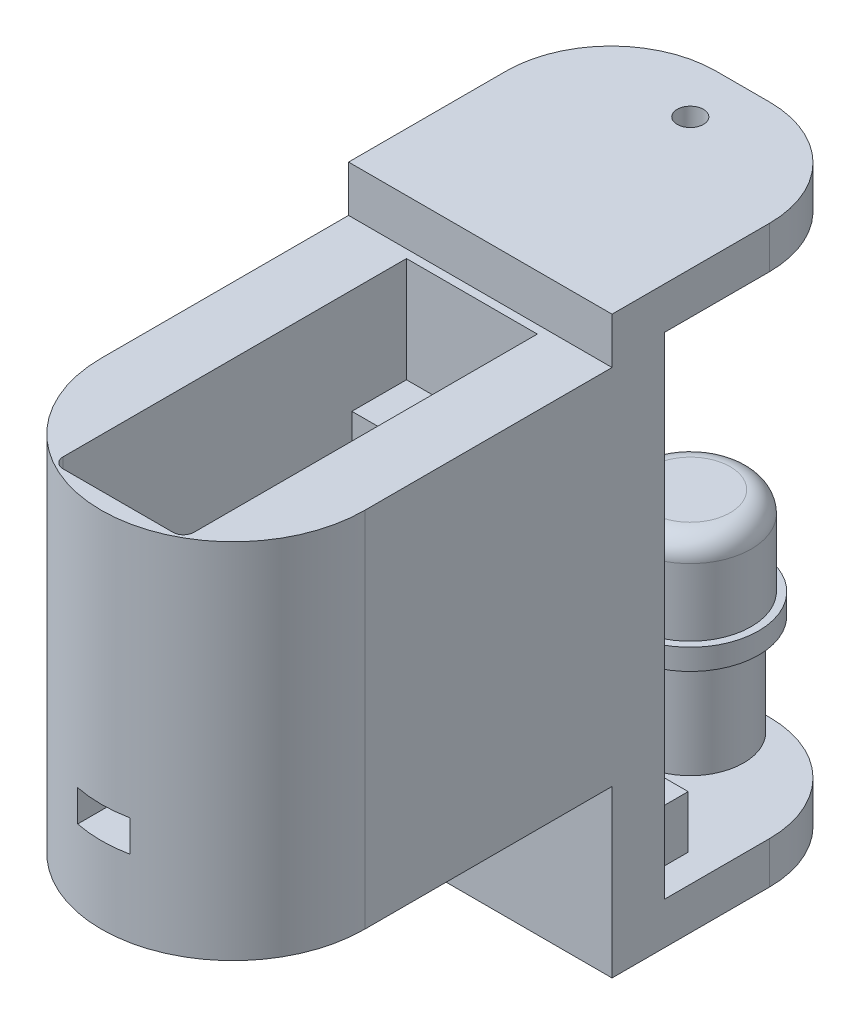
SolidWorks part; units mm, degrees
ref_plane "Front Plane" through (0, 0, 0) normal (0, 0, 1) x (1, 0, 0)
ref_plane "Top Plane" through (0, 0, 0) normal (0, 1, 0) x (1, 0, 0)
ref_plane "Right Plane" through (0, 0, 0) normal (1, 0, 0) x (0, 0, -1)
sketch "Sketch4" plane through (0, 0, 0) normal (0, 0, 1) x (1, 0, 0)
  line L1 (-6.23, -9.975) -> (6.23, -9.975)
  line L2 (-6.23, -9.975) -> (-6.23, 7.275)
  line L3 (-6.23, 7.275) -> (6.23, 7.275)
  line L4 (6.23, -9.975) -> (6.23, 7.275)
  point P4 (0, 7.275)
  dimension "D1" = 12.46
  dimension "D2" = 17.25
  dimension "D3" = 9.975
extrude "Boss-Extrude3" add sketch "Sketch4" along normal blind 6
sketch "Sketch8" plane through (0, -9.975, 0) normal (0, -1, 0) x (-1, 0, 0)
  circle A0 centre (0, -23.55) radius 12.5468
  circle A1 centre (0, -23.55) radius 11.15
  dimension "D1" = 22.3
  dimension "D2" = 23.55
extrude "Boss-Extrude6" add sketch "Sketch8" along normal blind 7.3 and the other way up to surface (17.25 mm away) other way up to face at (0, 7.275, 3)
sketch "Sketch5" plane through (0, 7.275, 0) normal (0, 1, 0) x (1, 0, 0)
  line L8 (12.5468, -23.55) -> (12.5468, 0)
  line L9 (12.5468, 0) -> (6.23, 0)
  line L10 (-12.5468, -23.55) -> (-12.5468, 0)
  line L11 (-12.5468, 0) -> (-6.23, 0)
  line L12 (-6.23, 0) -> (-6.23, -29.7)
  line L14 (6.23, -29.7) -> (6.23, 0)
  line L15 (-6.23, -29.7) -> (6.23, -29.7)
  line L16 (6.23, -6) -> (-6.23, -6) construction
  circle A0 centre (0, -23.55) radius 12.5468 construction
  arc A1 (-12.5468, -23.55) -> (12.5468, -23.55) centre (0, -23.55) ccw
  dimension "D1" = 23.7
  dimension "D2" = 23.55
extrude "Boss-Extrude4" add sketch "Sketch5" against normal up to surface (17.25 mm away) up to face at (0, -9.975, 3)
sketch "Sketch6" plane through (0, 7.275, 0) normal (0, 1, 0) x (1, 0, 0)
  line L0 (6.23, -6) -> (-6.23, -6) construction
  line L3 (6.23, -29.7) -> (-6.23, -29.7) construction
  circle A0 centre (0, -3.6) radius 0.5
  circle A1 centre (0, -32.1) radius 0.5
  dimension "D1" = 1
  dimension "D3" = 1
  dimension "D2" = 2.4
  dimension "D4" = 2.4
extrude "Cut-Extrude1" cut sketch "Sketch6" against normal blind 15
chamfer "Chamfer1" distance 0.5 angle 60 2 edges at (0, 7.275, 4.1) (0, 7.275, 32.6)
sketch "Sketch10" plane through (0, 7.275, 0) normal (0, 1, 0) x (1, 0, 0)
  line L1 (-6.23, -6) -> (6.23, -6)
  line L2 (-6.23, -6) -> (-6.23, -29.7)
  line L3 (-6.23, -29.7) -> (6.23, -29.7)
  line L4 (6.23, -6) -> (6.23, -29.7)
extrude "Cut-Extrude3" cut sketch "Sketch10" against normal up to surface (17.25 mm away) up to face at (0, -9.975, 27.1007)
ref_plane "Plane1" through (0, 0, 36.0968) normal (0, 0, 1) x (1, 0, 0)
sketch "Sketch11" plane through (0, 0, 36.0968) normal (0, 0, 1) x (1, 0, 0)
  line L0 (-11.15, -9.975) -> (11.15, -9.975) construction
  line L1 (-2.5, -6.975) -> (2.5, -6.975)
  line L2 (-2.5, -6.975) -> (-2.5, -9.975)
  line L3 (-2.5, -9.975) -> (2.5, -9.975)
  line L4 (2.5, -6.975) -> (2.5, -9.975)
  point P4 (0, -6.975)
  dimension "D1" = 0
  dimension "D2" = 5
  dimension "D3" = 3
extrude "Cut-Extrude4" cut sketch "Sketch11" against normal up to next
sketch "Sketch13" plane through (0, -17.275, 0) normal (0, -1, 0) x (1, 0, 0)
  line L0 (-12.5468, 23.55) -> (-12.5468, 0)
  line L1 (-12.5468, 0) -> (12.5468, 0)
  line L2 (12.5468, 0) -> (12.5468, 23.55)
  arc A0 (-12.5468, 23.55) -> (12.5468, 23.55) centre (0, 23.55) ccw
  point P3 (0, 0)
extrude "Boss-Extrude7" add sketch "Sketch13" against normal up to surface (7.3 mm away) up to face at (6.0145, -9.975, 27.3356)
sketch "Sketch15" plane through (0, 7.275, 0) normal (0, 1, 0) x (1, 0, 0)
  line L0 (-12.5468, 0) -> (12.5468, 0)
  line L1 (12.5468, 0) -> (12.5468, -23.55)
  line L2 (-12.5468, 0) -> (-12.5468, -23.55)
  line L3 (6.23, -6) -> (6.23, -29.7) construction
  line L4 (-6.23, -0.8) -> (6.23, -0.8)
  line L5 (-6.23, -0.8) -> (-6.23, -33.5)
  line L6 (-5.23, -34.5) -> (5.23, -34.5)
  line L7 (6.23, -0.8) -> (6.23, -33.5)
  arc A0 (-12.5468, -23.55) -> (12.5468, -23.55) centre (0, -23.55) ccw
  circle A1 centre (0, -3.6) radius 0.5 construction
  arc A2 (5.23, -34.5) -> (6.23, -33.5) centre (5.23, -33.5) ccw
  arc A3 (-6.23, -33.5) -> (-5.23, -34.5) centre (-5.23, -33.5) ccw
  point P15 (0, -0.8)
  dimension "D1" = 0.8
  dimension "D3" = 1
  dimension "D2" = 2.8
  dimension "D4" = 0
  dimension "D5" = 34.5
extrude "Boss-Extrude9" add sketch "Sketch15" along normal blind 10
sketch "Sketch20" plane through (0, -17.275, 0) normal (0, -1, 0) x (1, 0, 0)
  circle A0 centre (0, 23.55) radius 7.15
  circle A1 centre (0, 23.55) radius 11.15
  circle A2 centre (0, 23.55) radius 11.15 construction
  dimension "D1" = 14.3
extrude "Boss-Extrude11" add sketch "Sketch20" against normal up to surface (7.3 mm away) up to face at (-6.0145, -9.975, 27.3356)
sketch "Sketch21" plane through (0, -17.275, 0) normal (0, -1, 0) x (1, 0, 0)
  circle A0 centre (0, 23.55) radius 7.15
  circle A1 centre (0, 23.55) radius 10.15
  circle A2 centre (0, 23.55) radius 7.15 construction
  dimension "D1" = 20.3
extrude "Cut-Extrude7" cut sketch "Sketch21" against normal blind 1.3
sketch "Sketch17" plane through (12.5468, 4.7282, 0) normal (-1, 0, 0) x (0, 1, 0)
  line L0 (16.9468, 25) -> (16.9468, 0)
  line L1 (16.9468, 0) -> (-37.8032, 0)
  line L2 (-37.8032, 0) -> (-37.8032, 25)
  line L3 (-37.8032, 25) -> (-33.8032, 25)
  line L4 (-33.8032, 25) -> (-33.8032, 5)
  line L5 (-33.8032, 5) -> (12.9468, 5)
  line L6 (12.9468, 5) -> (12.9468, 25)
  line L7 (12.9468, 25) -> (16.9468, 25)
  line L8 (-22.0032, -23.55) -> (-22.0032, 0) construction
  line L10 (12.5468, 0) -> (12.5468, -23.55) construction
  dimension "D1" = 4
  dimension "D2" = 0.4
  dimension "D3" = 4
  dimension "D4" = 25
  dimension "D5" = 5
  dimension "D6" = 15.8
extrude "Boss-Extrude10" add sketch "Sketch17" along normal up to surface (25.0936 mm away) up to face at (-12.5468, 0, 11.775)
sketch "Sketch18" plane through (0, 17.675, 0) normal (0, -1, 0) x (0, 0, 1)
  line L0 (-25, -12.5468) -> (-25, 12.5468) construction
  line L1 (-25, 6.2191) -> (-5, 6.2191)
  line L2 (-25, 6.2191) -> (-25, -6.2191)
  line L3 (-25, -6.2191) -> (-5, -6.2191)
  line L4 (-5, 6.2191) -> (-5, -6.2191)
  line L5 (-5, -12.5468) -> (-5, 12.5468) construction
  point P6 (-25, 0)
  point P7 (-25, 0)
  dimension "D1" = 0
extrude "Cut-Extrude5" cut sketch "Sketch18" against normal blind 2
sketch "Sketch19" plane through (0, 19.675, 0) normal (0, -1, 0) x (0, 0, 1)
  line L0 (-25, -12.5468) -> (-25, 12.5468) construction
  circle A0 centre (-20, 0) radius 1.25
  dimension "D1" = 2.5
  dimension "D2" = 5
extrude "Cut-Extrude6" cut sketch "Sketch19" against normal through all both and the other way through all
fillet "Fillet1" radius 10 4 edges at (-12.5468, 19.675, -25) (12.5468, 19.675, -25) (-12.5468, -31.075, -25) (12.5468, -31.075, -25)
ref_plane "Plane2" through (0, 0, 0) normal (1, 0, 0) x (0, 0, -1)
ref_plane "Plane3" through (0, 0, 0) normal (0, -1, 0) x (-1, 0, 0)
sketch "Sketch22" plane through (0, -29.075, 0) normal (0, 1, 0) x (0, 0, -1)
  circle A0 centre (20, 0) radius 5.8
  dimension "D1" = 11.6
extrude "Boss-Extrude12" add sketch "Sketch22" along normal blind 20
fillet "Fillet2" radius 2 1 edges at (-5.8, -9.075, -20)
sketch "Sketch23" plane through (0, -29.075, 0) normal (0, 1, 0) x (0, 0, -1)
  circle A0 centre (20, 0) radius 5.08
  circle A1 centre (20, 0) radius 5.9309
  dimension "D1" = 10.16
extrude "Cut-Extrude8" cut sketch "Sketch23" along normal blind 11.6
sketch "Sketch24" plane through (0, -17.475, 0) normal (0, -1, 0) x (0, 0, 1)
  circle A0 centre (-20, 0) radius 6.5
extrude "Boss-Extrude13" add sketch "Sketch24" along normal blind 2
sketch "Sketch25" plane through (0, -33.075, 0) normal (0, -1, 0) x (0, 0, 1)
  circle A0 centre (-20, 0) radius 1.25
extrude "Boss-Extrude14" add sketch "Sketch25" against normal blind 2
sketch "Sketch26" plane through (0, -29.075, 0) normal (0, 1, 0) x (0, 0, -1)
  line L0 (5, -12.5468) -> (5, 12.5468) construction
  line L1 (5, -9.7968) -> (10, -9.7968)
  line L2 (5, -9.7968) -> (5, -6.7968)
  line L3 (5, -6.7968) -> (10, -6.7968)
  line L4 (10, -9.7968) -> (10, -6.7968)
  line L6 (5, -5.2808) -> (10, -5.2808)
  line L7 (5, -5.2808) -> (5, -2.2808)
  line L8 (5, -2.2808) -> (10, -2.2808)
  line L9 (10, -5.2808) -> (10, -2.2808)
  line L10 (5, -12.5468) -> (15, -12.5468) construction
  dimension "D1" = 1.516
  dimension "D2" = 3
  dimension "D3" = 3
  dimension "D4" = 0
  dimension "D5" = 5
  dimension "D6" = 2.75
extrude "Boss-Extrude15" add sketch "Sketch26" along normal blind 5
